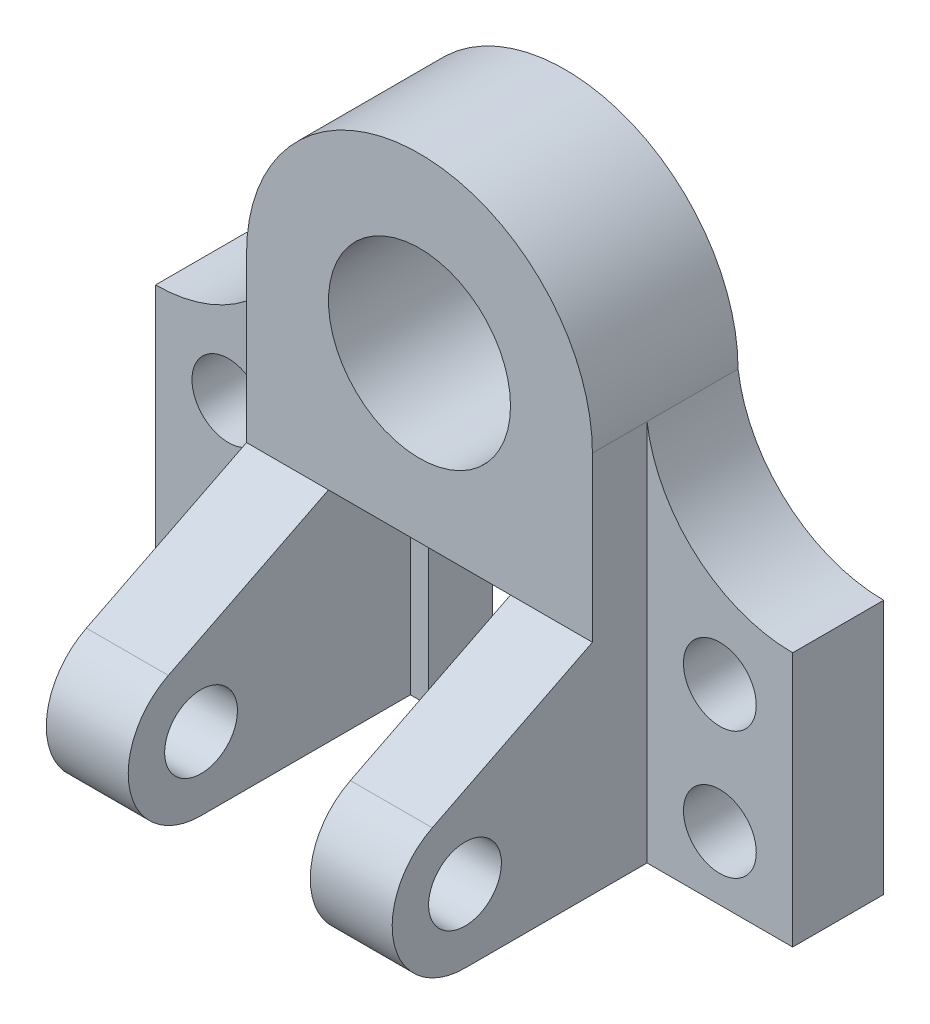
SolidWorks part; units mm, degrees
ref_plane "Front Plane" through (0, 0, 0) normal (0, 0, 1) x (1, 0, 0)
ref_plane "Top Plane" through (0, 0, 0) normal (0, 1, 0) x (1, 0, 0)
ref_plane "Right Plane" through (0, 0, 0) normal (1, 0, 0) x (0, 0, -1)
sketch "Sketch1" plane through (0, 0, 0) normal (0, 0, 1) x (1, 0, 0)
  line L0 (0, 77.9671) -> (0, -75.7489) construction
  line L1 (-59.4457, 0) -> (91.8303, 0) construction
  line L2 (-38, 0) -> (-38, -36)
  line L3 (-38, -36) -> (38, -36)
  line L4 (38, -36) -> (38, 0)
  arc A0 (38, 0) -> (-38, 0) centre (0, 0) ccw
  circle A1 centre (0, 0) radius 20
extrude "Boss-Extrude1" add sketch "Sketch1" along normal blind 32
ref_plane "Plane5" [suppressed] through (-38, -36, 0) normal (0, -1, 0) x (-1, 0, 0)
sketch "Sketch3" [suppressed] plane through (0, 0, 0) normal (0, 0, 1) x (1, 0, 0)
  line L0 (-38, -36) -> (-38, -84)
  line L1 (-38, -84) -> (-70, -84)
  line L2 (-70, -84) -> (-70, -28)
  line L3 (-38, 0) -> (-38, -36)
  arc A0 (-70, -28) -> (-38, 0) centre (-70, 4.2857) ccw
extrude "Boss-Extrude2" [suppressed] add sketch "Sketch3" along normal blind 20
hole_wizard "Ø16.0mm Dowel Hole1" positions "Sketch11" profile "Sketch10" hole size "Ø16.0" standard "ANSI Metric"
sketch "Sketch11" plane through (0, 0, 20) normal (0, 0, 1) x (1, 0, 0)
  line L0 (-70, -28) -> (-70, -84) construction
  line L5 (-70, -84) -> (-38, -84) construction
  point P0 (-54, -42)
  dimension "D1" = 16
  dimension "D2" = 42
sketch "Sketch10" plane through (-54, -42, 20) normal (1, 0, 0) x (0, -1, 0)
  line L0 (0, 0) -> (0, 20)
  line L1 (0, 20) -> (8, 20)
  line L2 (8, 20) -> (8, 0)
  line L5 (8, 0) -> (0, 0)
  line L11 (0, -6.35) -> (0, 107.95) construction
  dimension "Thru Hole Dia." = 16
  dimension "Thru Hole Depth" = 20
pattern_linear "LPattern2" [suppressed] count 2 spacing 28
mirror "Mirror3" [suppressed] about plane through (0, 0, 0) normal (1, 0, 0)
hole_wizard "Ø16.0mm Dowel Hole2" positions "Sketch14" profile "Sketch13" hole size "Ø16.0" standard "ANSI Metric"
sketch "Sketch14" plane through (0, 0, 20) normal (0, 0, 1) x (1, 0, 0)
  line L0 (70, -28) -> (70, -84) construction
  line L1 (70, -84) -> (38, -84) construction
  point P0 (54, -42)
  dimension "D1" = 16
  dimension "D2" = 42
sketch "Sketch13" plane through (54, -42, 20) normal (1, 0, 0) x (0, -1, 0)
  line L0 (0, 0) -> (0, 20)
  line L1 (0, 20) -> (8, 20)
  line L2 (8, 20) -> (8, 0)
  line L5 (8, 0) -> (0, 0)
  line L11 (0, -6.35) -> (0, 107.95) construction
  dimension "Thru Hole Dia." = 16
  dimension "Thru Hole Depth" = 20
pattern_linear "LPattern4" [suppressed] count 2 spacing 28
sketch "Sketch15" plane through (0, 0, 0) normal (0, 0, 1) x (1, 0, 0)
  line L0 (-38, -36) -> (-38, -84)
  line L1 (-38, -84) -> (-70, -84)
  line L2 (-70, -84) -> (-70, -28)
  line L3 (-70, -28) -> (-38, -28)
  line L4 (-38, 0) -> (-38, -36) construction
  line L5 (-38, 0) -> (-38, -28)
  arc A0 (-70, -28) -> (-38, 0) centre (-70, 4.2857) ccw
extrude "Boss-Extrude3" add sketch "Sketch15" along normal blind 20 contours L3 L5 A0
sketch "Sketch16" plane through (0, 0, 0) normal (0, 0, 1) x (1, 0, 0)
  line L0 (-38, -28) -> (-38, -84)
  line L1 (-38, -84) -> (-70, -84)
  line L2 (-70, -84) -> (-70, -28)
  line L3 (-70, -28) -> (-38, -28)
extrude "Boss-Extrude4" add sketch "Sketch16" along normal blind 20
hole_wizard "Ø16.0mm Dowel Hole3" positions "Sketch18" profile "Sketch19" hole size "Ø16.0" standard "ANSI Metric" end condition through all
sketch "Sketch18" plane through (0, 0, 20) normal (0, 0, 1) x (1, 0, 0)
  line L0 (-70, -28) -> (-70, -84) construction
  line L2 (-70, -84) -> (-38, -84) construction
  point P0 (-54, -42)
  point P9 (-463.1559, 151.13)
  dimension "D1" = 16
  dimension "D2" = 42
sketch "Sketch19" plane through (-54, -42, 20) normal (1, 0, 0) x (0, -1, 0)
  line L0 (0, 0) -> (0, 20)
  line L1 (0, 20) -> (8, 20)
  line L2 (8, 20) -> (8, 0)
  line L5 (8, 0) -> (0, 0)
  line L11 (0, -6.35) -> (0, 107.95) construction
  dimension "Thru Hole Dia." = 16
  dimension "Thru Hole Depth" = 20
pattern_linear "LPattern5" count 2 spacing 28 along (0, -1, 0) of "Ø16.0mm Dowel Hole3"
mirror "Mirror5" about plane through (0, 0, 0) normal (1, 0, 0) of "Boss-Extrude4", "Boss-Extrude3", "LPattern5", "Ø16.0mm Dowel Hole3"
sketch "Sketch25" plane through (-38, 0, 0) normal (1, 0, 0) x (0, 0, -1)
  line L0 (0, -84) -> (-60, -84)
  line L2 (0, -84) -> (0, -36)
  line L3 (0, -28) -> (0, -84) construction
  line L4 (0, -36) -> (-32, -36)
  line L5 (-32, -36) -> (-67.1916, -53.7073)
  arc A0 (-67.1916, -53.7073) -> (-60, -84) centre (-60, -68) ccw
  circle A1 centre (-60, -68) radius 8
  dimension "D1" = 60
  dimension "D2" = 16
  dimension "D3" = 16
extrude "Boss-Extrude6" add sketch "Sketch25" along normal blind 18
sketch "Sketch26" plane through (-20, 0, 0) normal (1, 0, 0) x (0, 0, -1)
  line L0 (0, -84) -> (-14, -84)
  line L1 (-60, -84) -> (0, -84) construction
  line L2 (0, -84) -> (0, -36)
  line L3 (0, -36) -> (-14, -36)
  line L4 (0, -36) -> (-32, -36) construction
  line L5 (-14, -36) -> (-14, -84)
extrude "Boss-Extrude7" add sketch "Sketch26" along normal blind 4
mirror "Mirror6" about plane through (0, 0, 0) normal (1, 0, 0) of "Boss-Extrude6", "Boss-Extrude7"
